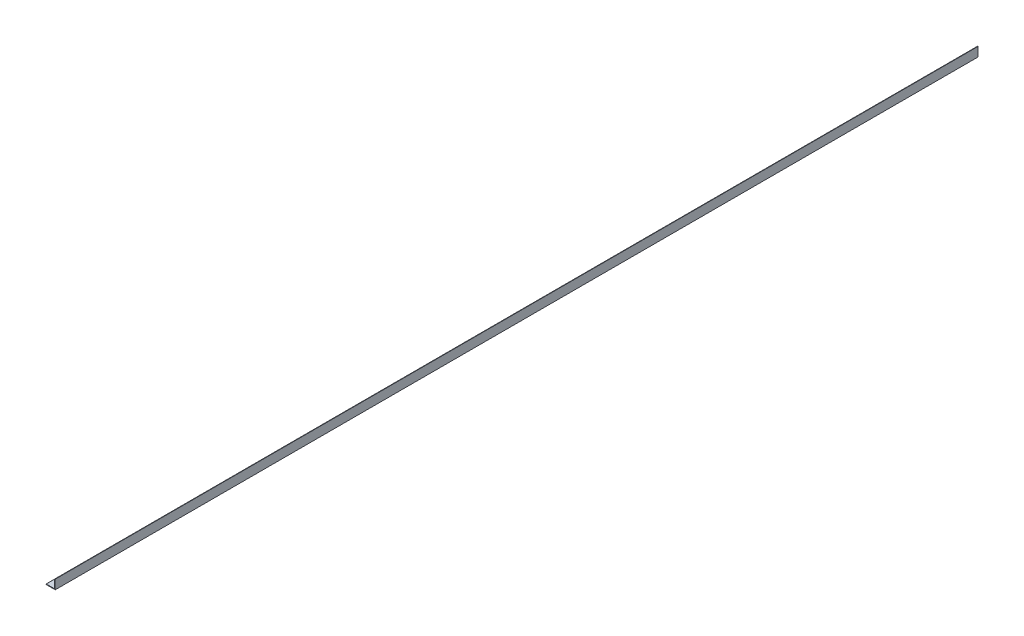
SolidWorks part; units mm, degrees
ref_plane "Front Plane" through (0, 0, 0) normal (0, 0, 1) x (1, 0, 0)
ref_plane "Top Plane" through (0, 0, 0) normal (0, 1, 0) x (1, 0, 0)
ref_plane "Right Plane" through (0, 0, 0) normal (1, 0, 0) x (0, 0, -1)
sketch "Sketch0" plane through (0, 0, 0) normal (0, 0, 1) x (1, 0, 0)
  line L0 (-12.7, -12.7) -> (12.7, -12.7)
  line L1 (12.7, -12.7) -> (12.7, 12.7)
  line L2 (12.7, 0) -> (0, 0) construction
  line L3 (0, 0) -> (0, -12.7) construction
  line L4 (11.1125, -9.5377) -> (11.1125, 12.7) construction
  line L5 (9.5377, -11.1125) -> (-12.7, -11.1125) construction
  arc A0 (11.1125, -9.5377) -> (9.5377, -11.1125) centre (9.5377, -9.5377) cw
  point P3 (10.6513, -10.6513)
  dimension "Inside Corner Radius" = 1.5748
  dimension "Outside Height" = 25.4
  dimension "Inside Height" = 23.8125
  dimension "Inside Width" = 23.8125
  dimension "Wall Thickness" = 1.5875
  dimension "D1" = 1.5875
  dimension "Outside Width" = 25.4
sketch "Sketch1" plane through (0, 0, 0) normal (1, 0, 0) x (0, 0, -1)
  line L0 (914.4, 0) -> (-914.4, 0)
  point P4 (0, 0)
  dimension "Length" = 1828.8
sketch "Sketch2" plane through (0, 0, 0) normal (0, 0, 1) x (1, 0, 0)
  line L0 (-12.7, -12.7) -> (12.7, -12.7)
  line L1 (12.7, -12.7) -> (12.7, 12.7)
  line L2 (12.7, 12.7) -> (11.1125, 12.7) construction
  line L3 (11.1125, 11.9062) -> (11.1125, -9.5377)
  line L4 (9.5377, -11.1125) -> (-11.9062, -11.1125)
  line L5 (-12.7, -12.7) -> (-12.7, -11.1125) construction
  line L6 (11.9062, 12.7) -> (12.7, 12.7)
  line L7 (-12.7, -11.9062) -> (-12.7, -12.7)
  line L8 (12.7, 0) -> (0, 0) construction
  line L9 (0, 0) -> (0, -12.7) construction
  arc A0 (11.1125, 11.9062) -> (11.9062, 12.7) centre (11.9062, 11.9062) cw
  arc A1 (-12.7, -11.9062) -> (-11.9062, -11.1125) centre (-11.9062, -11.9062) cw
  arc A2 (11.1125, -9.5377) -> (9.5377, -11.1125) centre (9.5377, -9.5377) cw
  dimension "Inside Radius" = 1.5748
  dimension "Height" = 25.4
  dimension "Width" = 25.4
  dimension "Thickness" = 1.5875
extrude "Boss-Extrude1" add sketch "Sketch2" along normal mid plane 2540
sketch "Break Locations" plane through (0, 0, 0) normal (1, 0, 0) x (0, 0, -1)
  line L0 (-1244.092, 0) -> (1244.092, 0)
  line L1 (-1270, -12.7) -> (-1270, 12.7) construction
  line L2 (1270, -12.7) -> (1270, 12.7) construction
  point P0 (-1248.41, 0)
  point P1 (1248.41, 0)
  point P10 (0, 0)
  point P11 (1244.092, 0)
  point P13 (-1244.092, 0)
  dimension "D1" = 21.59
  dimension "D2" = 21.59
  dimension "D3" = 25.908
hole_wizard "1/4-20 Tapped Hole1" positions "Sketch3" profile "Sketch4" tap size "1/4-20" standard "ANSI Inch" end condition through all
sketch "Sketch3" plane through (0, -11.1125, 0) normal (0, 1, 0) x (1, 0, 0)
  line L2 (11.1125, -1270) -> (11.1125, 1270) construction
  line L3 (9.5377, -1270) -> (-11.9062, -1270) construction
  point P0 (-1.5875, -1017.524)
  point P3 (-1.5875, -1017.524)
  point P11 (-1.5875, -561.848)
  point P13 (-1.5875, 349.504)
  point P15 (-1.5875, -106.172)
  dimension "D1" = 12.7
  dimension "D2" = 252.476
  dimension "D3" = 455.676
  dimension "D4" = 455.676
  dimension "D5" = 455.676
cosmetic thread "Hole Thread1" parameters "D2"=6.35
sketch "Sketch4" plane through (-1.5875, -11.1125, 1017.524) normal (1, 0, 0) x (0, 0, 1)
  line L0 (0, 0) -> (0, 1.5875)
  line L1 (0, 1.5875) -> (2.5527, 1.5875)
  line L2 (2.5527, 1.5875) -> (2.5527, 0)
  line L5 (2.5527, 0) -> (0, 0)
  line L11 (0, -6.35) -> (0, 107.95) construction
  dimension "Thru Tap Drill Dia." = 5.1054
  dimension "Thru Tap Drill Depth" = 1.5875
cosmetic thread "Hole Thread2" parameters "D2"=6.35
cosmetic thread "Hole Thread3" parameters "D2"=6.35
cosmetic thread "Hole Thread4" parameters "D2"=6.35
sketch "Sketch5" plane through (0, -11.1125, 0) normal (0, 1, 0) x (1, 0, 0)
  line L0 (-1.5875, -1057.275) -> (-1.5875, -1076.325) construction
  line L1 (1.4605, -1057.275) -> (1.4605, -1076.325)
  line L2 (-4.6355, -1057.275) -> (-4.6355, -1076.325)
  line L3 (9.5377, -1270) -> (-11.9062, -1270) construction
  line L4 (11.1125, -1270) -> (11.1125, 1270) construction
  line L5 (-1.5875, -641.35) -> (-1.5875, -660.4) construction
  line L6 (1.4605, -641.35) -> (1.4605, -660.4)
  line L7 (-4.6355, -641.35) -> (-4.6355, -660.4)
  line L8 (-57.0785, 0) -> (40.0941, 0) construction
  line L9 (-1.5875, 317.5) -> (-1.5875, 336.55) construction
  line L10 (1.4605, 317.5) -> (1.4605, 336.55)
  line L11 (-4.6355, 317.5) -> (-4.6355, 336.55)
  line L12 (-1.5875, 717.55) -> (-1.5875, 1092.2) construction
  line L13 (1.4605, 717.55) -> (1.4605, 1092.2)
  line L14 (-4.6355, 717.55) -> (-4.6355, 1092.2)
  line L15 (9.5377, 1270) -> (-11.9062, 1270) construction
  arc A0 (1.4605, -1057.275) -> (-4.6355, -1057.275) centre (-1.5875, -1057.275) ccw
  arc A1 (-4.6355, -1076.325) -> (1.4605, -1076.325) centre (-1.5875, -1076.325) ccw
  arc A2 (1.4605, -641.35) -> (-4.6355, -641.35) centre (-1.5875, -641.35) ccw
  arc A3 (-4.6355, -660.4) -> (1.4605, -660.4) centre (-1.5875, -660.4) ccw
  arc A4 (1.4605, 317.5) -> (-4.6355, 317.5) centre (-1.5875, 317.5) cw
  arc A5 (-4.6355, 336.55) -> (1.4605, 336.55) centre (-1.5875, 336.55) cw
  arc A6 (1.4605, 717.55) -> (-4.6355, 717.55) centre (-1.5875, 717.55) cw
  arc A7 (-4.6355, 1092.2) -> (1.4605, 1092.2) centre (-1.5875, 1092.2) cw
  point P2 (-1.5875, -1066.8)
  point P13 (-1.5875, -650.875)
  point P23 (-1.5875, 327.025)
  point P30 (-1.5875, 904.875)
  dimension "D2" = 3.048
  dimension "D5" = 3.048
  dimension "D12" = 3.048
  dimension "D13" = 3.048
  dimension "D1" = 19.05
  dimension "D3" = 203.2
  dimension "D4" = 12.7
  dimension "D6" = 19.05
  dimension "D7" = 609.6
  dimension "D8" = 317.5
  dimension "D9" = 177.8
  dimension "D10" = 12.7
  dimension "D11" = 12.7
extrude "Cut-Extrude1" cut sketch "Sketch5" against normal through all
equation "\"D1@Break Locations\" = .85 * \"Height@Sketch2\""
equation "\"D2@Break Locations\"=\"D1@Break Locations\""
equation "\"Thickness@Sketch2\"=\"wall thickness@sketch0\""
equation "\"Height@Sketch2\"=\"outside height@sketch0\""
equation "\"Width@Sketch2\"=\"outside width@sketch0\""
equation "\"Inside Radius@Sketch2\"=\"inside corner radius@sketch0\""
equation "\"D3@Break Locations\"=\"D2@Break Locations\"*1.2"
equation "\"D1@Sketch0\"=\"Wall Thickness@Sketch0\""
